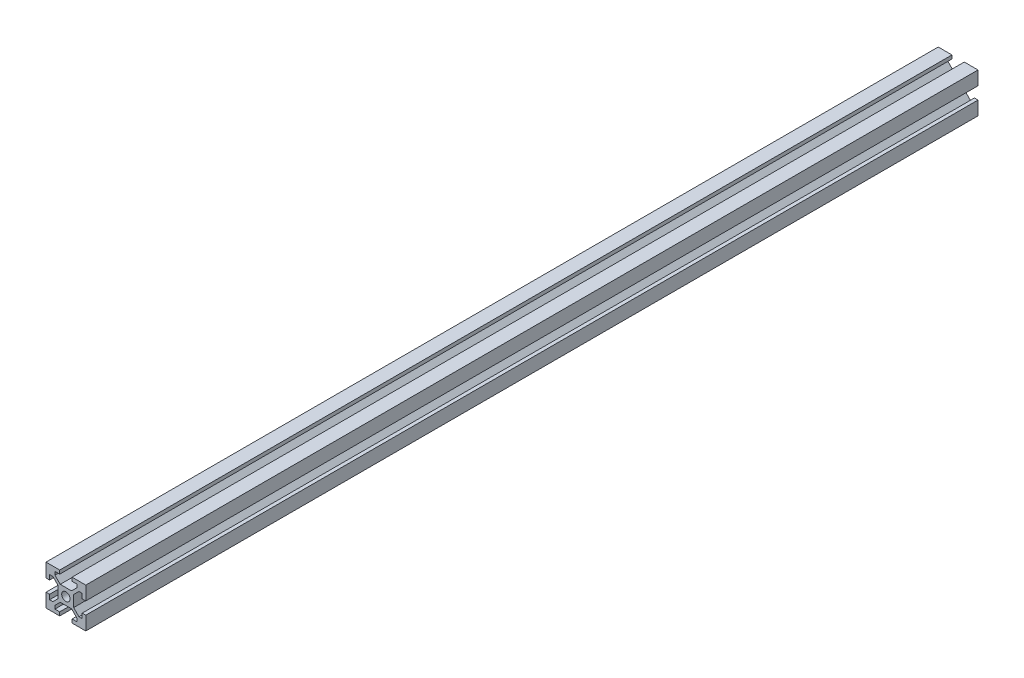
SolidWorks part; units mm, degrees
ref_plane "Front Plane" through (0, 0, 0) normal (0, 0, 1) x (1, 0, 0)
ref_plane "Top Plane" through (0, 0, 0) normal (0, 1, 0) x (1, 0, 0)
ref_plane "Right Plane" through (0, 0, 0) normal (1, 0, 0) x (0, 0, -1)
sketch "Sketch1" plane through (0, 0, 0) normal (0, 0, 1) x (1, 0, 0)
  line L0 (-3.1, 10) -> (-3.1, 8.2007)
  line L1 (-10, 10) -> (-3.1, 10)
  line L2 (-10, 10) -> (-10, 3.1)
  line L3 (-10, -10) -> (-3.1, -10)
  line L4 (10, 10) -> (10, 3.1)
  line L5 (-10, 10) -> (10, -10) construction
  line L6 (-10, -10) -> (10, 10) construction
  line L7 (-3.1, 8.2007) -> (-5.5, 8.2007)
  line L8 (-5.5, 8.2007) -> (-5.5, 6.5607)
  line L9 (-5.5, 6.5607) -> (-2.84, 3.9007)
  line L10 (-2.84, 3.9007) -> (2.84, 3.9007)
  line L11 (2.84, 3.9007) -> (5.5, 6.5607)
  line L12 (5.5, 6.5607) -> (5.5, 8.2007)
  line L13 (5.5, 8.2007) -> (3.1, 8.2007)
  line L14 (3.1, 8.2007) -> (3.1, 10)
  line L15 (-3.1, 8.2007) -> (3.1, 8.2007) construction
  line L16 (-5.5, 6.5607) -> (5.5, 6.5607) construction
  line L17 (3.1, 10) -> (10, 10)
  line L18 (8.2007, 3.1) -> (8.2007, 5.5)
  line L19 (8.2007, 5.5) -> (6.5607, 5.5)
  line L20 (6.5607, 5.5) -> (3.9007, 2.84)
  line L21 (3.9007, 2.84) -> (3.9007, -2.84)
  line L22 (3.9007, -2.84) -> (6.5607, -5.5)
  line L23 (6.5607, -5.5) -> (8.2007, -5.5)
  line L24 (8.2007, -5.5) -> (8.2007, -3.1)
  line L25 (8.2007, 3.1) -> (8.2007, -3.1) construction
  line L26 (6.5607, 5.5) -> (6.5607, -5.5) construction
  line L27 (10, 3.1) -> (8.2007, 3.1)
  line L28 (8.2007, -3.1) -> (10, -3.1)
  line L29 (3.1, -8.2007) -> (5.5, -8.2007)
  line L30 (5.5, -8.2007) -> (5.5, -6.5607)
  line L31 (5.5, -6.5607) -> (2.84, -3.9007)
  line L32 (2.84, -3.9007) -> (-2.84, -3.9007)
  line L33 (-2.84, -3.9007) -> (-5.5, -6.5607)
  line L34 (-5.5, -6.5607) -> (-5.5, -8.2007)
  line L35 (-5.5, -8.2007) -> (-3.1, -8.2007)
  line L36 (3.1, -8.2007) -> (-3.1, -8.2007) construction
  line L37 (5.5, -6.5607) -> (-5.5, -6.5607) construction
  line L38 (3.1, -10) -> (3.1, -8.2007)
  line L39 (-3.1, -8.2007) -> (-3.1, -10)
  line L40 (-8.2007, -3.1) -> (-8.2007, -5.5)
  line L41 (-8.2007, -5.5) -> (-6.5607, -5.5)
  line L42 (-6.5607, -5.5) -> (-3.9007, -2.84)
  line L43 (-3.9007, -2.84) -> (-3.9007, 2.84)
  line L44 (-3.9007, 2.84) -> (-6.5607, 5.5)
  line L45 (-6.5607, 5.5) -> (-8.2007, 5.5)
  line L46 (-8.2007, 5.5) -> (-8.2007, 3.1)
  line L47 (-8.2007, -3.1) -> (-8.2007, 3.1) construction
  line L48 (-6.5607, -5.5) -> (-6.5607, 5.5) construction
  line L49 (-10, -3.1) -> (-8.2007, -3.1)
  line L50 (-8.2007, 3.1) -> (-10, 3.1)
  line L51 (10, -3.1) -> (10, -10)
  line L52 (3.1, -10) -> (10, -10)
  line L53 (-10, -3.1) -> (-10, -10)
  point P0 (0, 0)
  point P8 (0, 8.2007)
  point P18 (0, 3.9007)
  dimension "D1" = 20
  dimension "D2" = 20
  dimension "D3" = 5.68
  dimension "D4" = 6.2
  dimension "D5" = 4.3
  dimension "D6" = 11
  dimension "D7" = 0.75
  dimension "D8" = 4
extrude "Boss-Extrude1" add sketch "Sketch1" along normal blind 448.61
sketch "Sketch2" plane through (0, 0, 448.61) normal (0, 0, 1) x (1, 0, 0)
  circle A0 centre (0, 0) radius 2.1
  dimension "D1" = 4.2
extrude "Cut-Extrude1" cut sketch "Sketch2" against normal through all
sketch "Sketch3" plane through (0, 3.9007, 0) normal (0, 1, 0) x (1, 0, 0)
  line L0 (0, 0) -> (0, -448.61) construction
  line L1 (2.84, -448.61) -> (-2.84, -448.61) construction
  circle A0 centre (0, -224.305) radius 2.1
  dimension "D1" = 4.2
extrude "Cut-Extrude2" cut sketch "Sketch3" against normal through all
